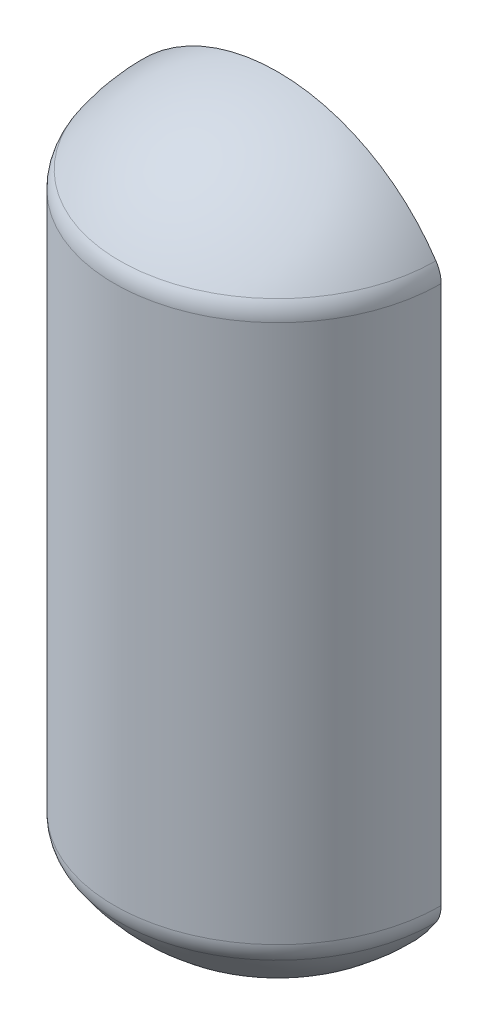
SolidWorks part; units mm, degrees
material "Custom Plastic"
ref_plane "Front Plane" through (0, 0, 0) normal (0, 0, 1) x (1, 0, 0)
ref_plane "Top Plane" through (0, 0, 0) normal (0, 1, 0) x (1, 0, 0)
ref_plane "Right Plane" through (0, 0, 0) normal (1, 0, 0) x (0, 0, -1)
sketch "Sketch1" plane through (0, 0, 0) normal (0, 0, 1) x (1, 0, 0)
  line L0 (0, 0) -> (0, 1200) construction
  line L1 (-133.985, 76.2) -> (133.985, 76.2) construction
  line L2 (-133.985, 0) -> (133.985, 0) construction
  line L3 (-133.985, 0) -> (-133.985, 1200) construction
  line L4 (-133.985, 1200) -> (133.985, 1200) construction
  line L5 (133.985, 0) -> (133.985, 1200) construction
  line L6 (-133.985, 0) -> (133.985, 1200) construction
  line L7 (-133.985, 1200) -> (133.985, 0) construction
  line L8 (-133.985, 685.1) -> (133.985, 685.1) construction
  line L9 (-133.985, 1123.8) -> (133.985, 1123.8) construction
  line L10 (-133.985, 608.9) -> (133.985, 608.9) construction
  line L11 (-133.985, 532.7) -> (133.985, 532.7) construction
  line L12 (-133.985, 608.9) -> (0, 608.9) construction
  line L13 (0, 608.9) -> (133.985, 608.9) construction
  line L14 (-133.985, 1123.8) -> (-133.985, 685.1)
  line L15 (133.985, 1123.8) -> (133.985, 685.1) construction
  line L16 (-133.985, 532.7) -> (-133.985, 76.2)
  line L17 (133.985, 532.7) -> (133.985, 76.2) construction
  line L18 (-130.81, 531.8223) -> (-130.81, 77.0777)
  line L19 (130.81, 531.8223) -> (130.81, 77.0777) construction
  line L20 (-130.81, 1122.9223) -> (-130.81, 685.9777)
  line L21 (130.81, 1122.9223) -> (130.81, 685.9777) construction
  line L22 (0, 612.075) -> (0, 608.9)
  line L23 (0, 605.725) -> (0, 608.9)
  line L24 (0, 3.175) -> (0, 0)
  line L25 (0, 1200) -> (0, 1196.825)
  line L26 (0, 1200) -> (0, 0)
  arc A0 (0, 0) -> (-133.985, 76.2) centre (0, 155.8951) cw
  arc A1 (0, 0) -> (133.985, 76.2) centre (0, 155.8951) ccw construction
  arc A2 (0, 1200) -> (133.985, 1123.8) centre (0, 1044.1049) cw construction
  arc A3 (0, 1200) -> (-133.985, 1123.8) centre (0, 1044.1049) ccw
  arc A4 (0, 608.9) -> (-133.985, 532.7) centre (0, 453.0049) ccw
  arc A5 (0, 608.9) -> (133.985, 532.7) centre (0, 453.0049) cw construction
  arc A6 (0, 608.9) -> (-133.985, 685.1) centre (0, 764.7951) cw
  arc A7 (0, 608.9) -> (133.985, 685.1) centre (0, 764.7951) ccw construction
  arc A8 (0, 605.725) -> (-130.81, 531.8223) centre (0, 453.0049) ccw
  arc A9 (0, 3.175) -> (-130.81, 77.0777) centre (0, 155.8951) cw
  arc A10 (0, 3.175) -> (130.81, 77.0777) centre (0, 155.8951) ccw construction
  arc A11 (0, 605.725) -> (130.81, 531.8223) centre (0, 453.0049) cw construction
  arc A12 (0, 612.075) -> (-130.81, 685.9777) centre (0, 764.7951) cw
  arc A13 (0, 1196.825) -> (-130.81, 1122.9223) centre (0, 1044.1049) ccw
  arc A14 (0, 1196.825) -> (130.81, 1122.9223) centre (0, 1044.1049) cw construction
  arc A15 (0, 612.075) -> (130.81, 685.9777) centre (0, 764.7951) ccw construction
  point P3 (0, 600)
  dimension "D3" = 76.2
  dimension "D1" = 1200
  dimension "D2" = 267.97
  dimension "D4" = 76.2
  dimension "D5" = 76.2
  dimension "D6" = 1200
  dimension "D7" = 591.1
  dimension "D8" = 76.2
  dimension "D9" = 3.175
  dimension "D10" = 3.175
revolve "Revolve1" add sketch "Sketch1" angle 180 about L0
fillet "Fillet1" radius 25.4 2 edges at (0, 76.2, 133.985) (0, 532.7, 133.985)
